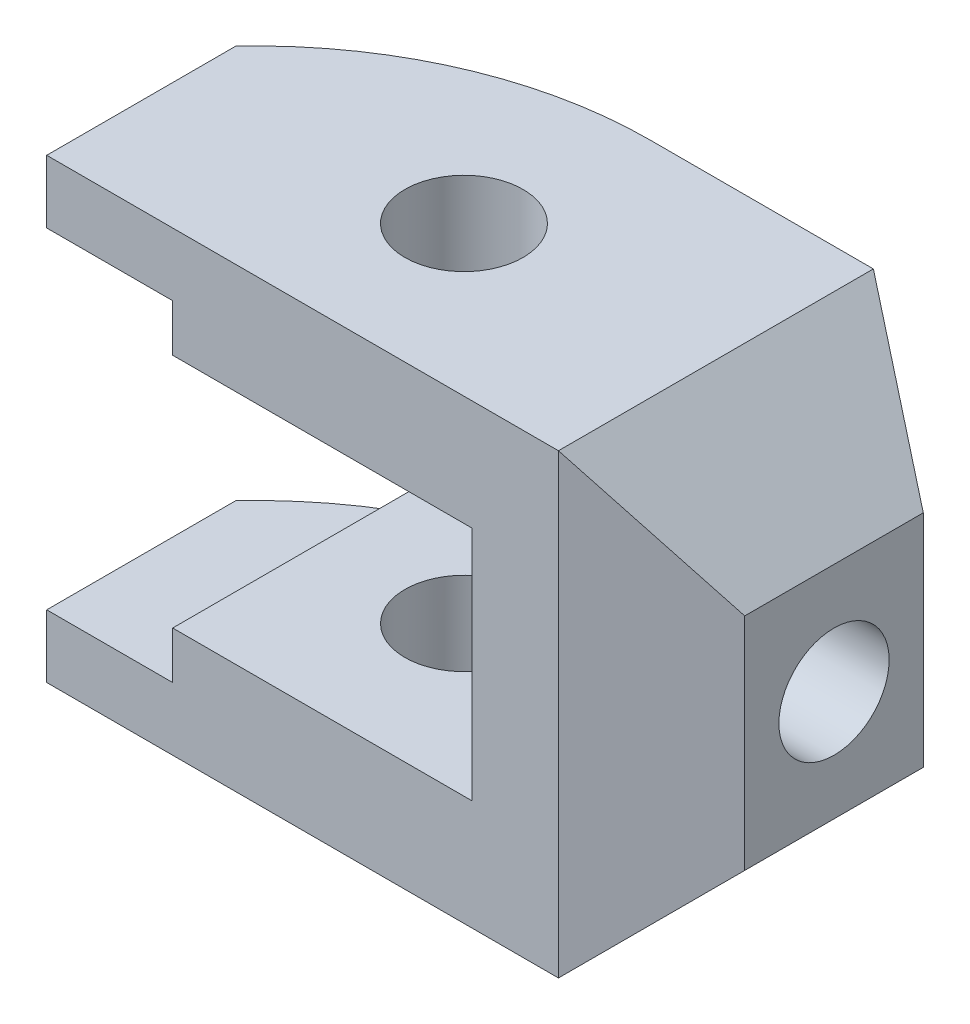
SolidWorks part; units mm, degrees
material "1060 Alloy"
ref_plane "Front Plane" through (0, 0, 0) normal (0, 0, 1) x (1, 0, 0)
ref_plane "Top Plane" through (0, 0, 0) normal (0, 1, 0) x (1, 0, 0)
ref_plane "Right Plane" through (0, 0, 0) normal (1, 0, 0) x (0, 0, -1)
sketch "Sketch1" plane through (0, 0, 0) normal (0, 1, 0) x (1, 0, 0)
  line L0 (0, -19) -> (0, 7.5) construction
  line L1 (-34, 0) -> (7.5, 0) construction
  line L2 (0, -19) -> (31, -19)
  line L3 (-34, -19) -> (-34, 5)
  line L4 (0, -19) -> (-34, -19)
  line L5 (31, -19) -> (46, -10.3397)
  line L6 (46, -10.3397) -> (46, 12.3397)
  line L7 (46, 12.3397) -> (31, 21)
  line L8 (31, 21) -> (2.6606, 21)
  line L9 (31, -19) -> (42.9903, -19) construction
  line L10 (31, 21) -> (42.9903, 21) construction
  circle A0 centre (0, 0) radius 7.5
  arc A1 (2.6606, 21) -> (-34, 5) centre (2.6606, -29) ccw
  point P4 (0, 0)
  point P10 (0, -19)
  point P19 (0, 0)
  point P20 (0, 0)
  point P21 (0, 0)
  dimension "D1" = 15
  dimension "D11" = 50
  dimension "D2" = 19
  dimension "D3" = 31
  dimension "D4" = 24
  dimension "D5" = 65
  dimension "D6" = 30
  dimension "D7" = 15
  dimension "D8" = 30
  dimension "D9" = 15
  dimension "D10" = 40
extrude "Boss-Extrude2" add sketch "Sketch1" along normal blind 58
sketch "Sketch4" plane through (0, 0, 0) normal (0, 0, 1) x (1, 0, 0)
  line L0 (31, 0) -> (46, 15)
  line L1 (46, 58) -> (46, 0) construction
  line L2 (46, 15) -> (46, 0)
  line L3 (46, 0) -> (31, 0)
  line L4 (31, 29) -> (46, 29) construction
  line L5 (31, 58) -> (31, 0) construction
  line L6 (31, 58) -> (46, 43)
  line L7 (46, 43) -> (46, 58)
  line L8 (46, 58) -> (31, 58)
  dimension "D1" = 45
extrude "Cut-Extrude1" cut sketch "Sketch4" against normal mid plane 58
sketch "Sketch6" plane through (0, 0, 0) normal (1, 0, 0) x (0, 0, -1)
  line L0 (-6, 29) -> (8, 29) construction
  line L3 (1, 36) -> (1, 22) construction
  line L8 (21, 58) -> (-19, 58) construction
  line L9 (-19, 58) -> (-19, 0) construction
  circle A0 centre (1, 29) radius 7
  dimension "D1" = 29
  dimension "D3" = 14
  dimension "D2" = 20
extrude "Cut-Extrude2" cut sketch "Sketch6" against normal mid plane 128
sketch "Sketch7" plane through (0, 0, 19) normal (0, 0, 1) x (1, 0, 0)
  line L0 (-1.5, 0) -> (-1.5, 58) construction
  line L1 (-34, 0) -> (31, 0) construction
  line L2 (-34, 58) -> (31, 58) construction
  line L3 (31, 29) -> (-34, 29) construction
  line L4 (31, 58) -> (31, 0) construction
  line L5 (-34, 58) -> (-34, 0) construction
  line L6 (-34, 50) -> (-18, 50)
  line L7 (-18, 50) -> (-18, 44)
  line L8 (-18, 44) -> (20, 44)
  line L9 (20, 44) -> (20, 14)
  line L10 (-18, 8) -> (-18, 14)
  line L11 (-18, 14) -> (20, 14)
  line L12 (-34, 8) -> (-18, 8)
  line L13 (-34, 50) -> (-34, 8)
  point P18 (20, 29)
  dimension "D1" = 8
  dimension "D2" = 6
  dimension "D3" = 16
  dimension "D4" = 11
extrude "Cut-Extrude3" cut sketch "Sketch7" against normal mid plane 128
equation "\"A\"= 58mm"
equation "\"B\"= 40mm"
equation "\"C\"= 65mm"
